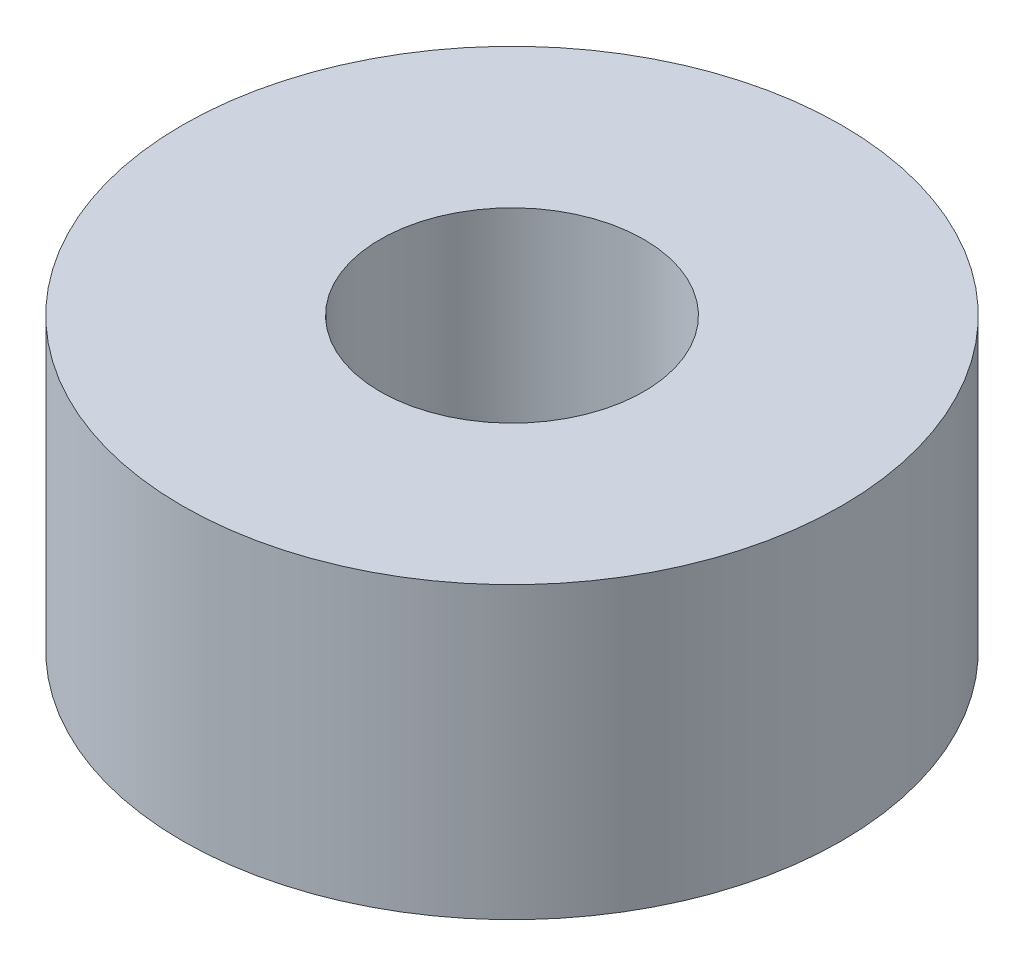
SolidWorks part; units mm, degrees
ref_plane "Front Plane" through (0, 0, 0) normal (0, 0, 1) x (1, 0, 0)
ref_plane "Top Plane" through (0, 0, 0) normal (0, 1, 0) x (1, 0, 0)
ref_plane "Right Plane" through (0, 0, 0) normal (1, 0, 0) x (0, 0, -1)
sketch "Sketch1" plane through (0, 0, 0) normal (0, 1, 0) x (1, 0, 0)
  circle A0 centre (0, 0) radius 10
  circle A1 centre (0, 0) radius 25
  dimension "D1" = 50
  dimension "D2" = 20
extrude "Boss-Extrude1" add sketch "Sketch1" along normal blind 22 contours A0
